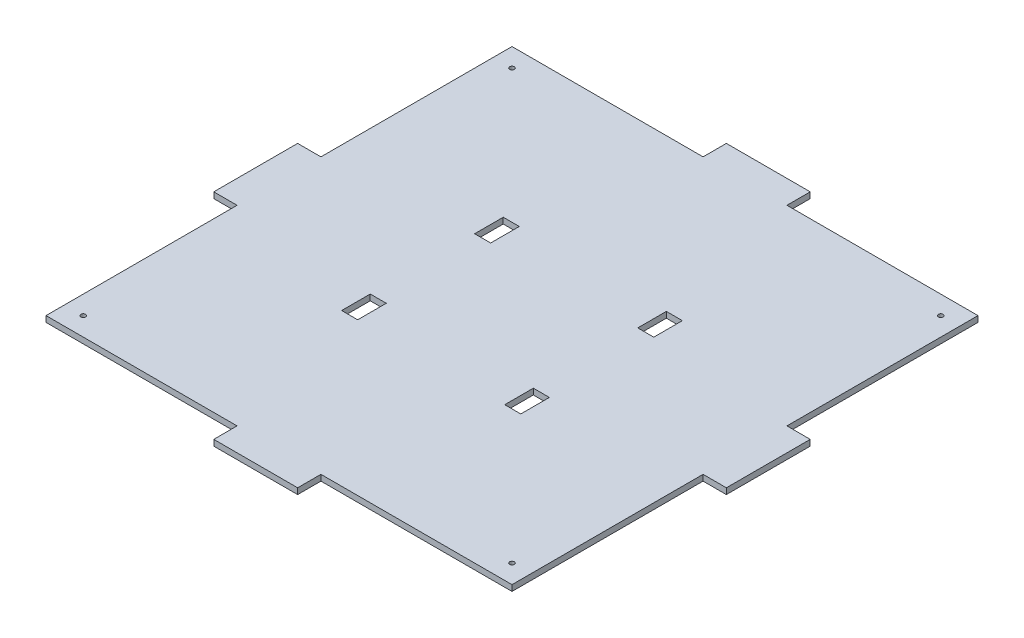
SolidWorks part; units mm, degrees
ref_plane "Front Plane" through (0, 0, 0) normal (0, 0, 1) x (1, 0, 0)
ref_plane "Top Plane" through (0, 0, 0) normal (0, 1, 0) x (1, 0, 0)
ref_plane "Right Plane" through (0, 0, 0) normal (1, 0, 0) x (0, 0, -1)
sketch "Sketch2" plane through (0, 0, 0) normal (0, 1, 0) x (1, 0, 0)
  line L1 (-125, -125) -> (125, -125)
  line L2 (-125, -125) -> (-125, 125)
  line L3 (-125, 125) -> (125, 125)
  line L4 (125, -125) -> (125, 125)
  line L5 (-125, -125) -> (125, 125) construction
  line L6 (-125, 125) -> (125, -125) construction
  point P0 (0, 0)
  dimension "D1" = 250
  dimension "250" = 250
extrude "Boss-Extrude1" add sketch "Sketch2" along normal blind 3.175
sketch "Sketch3" plane through (0, 3.175, 0) normal (0, 1, 0) x (1, 0, 0)
  line L0 (-125, 0) -> (125, 0) construction
  line L1 (-125, 125) -> (-125, -125) construction
  line L2 (125, -125) -> (125, 125) construction
  line L3 (-43.75, 125) -> (-43.75, -125) construction
  line L4 (125, 125) -> (-125, 125) construction
  line L5 (-125, -125) -> (125, -125) construction
  line L6 (0, 125) -> (0, -125) construction
  line L11 (-48.05, 28) -> (-39.45, 28)
  line L12 (-48.05, 28) -> (-48.05, 43.35)
  line L13 (-48.05, 43.35) -> (-39.45, 43.35)
  line L14 (-39.45, 28) -> (-39.45, 43.35)
  line L15 (-48.05, 28) -> (-39.45, 43.35) construction
  line L16 (-48.05, 43.35) -> (-39.45, 28) construction
  line L21 (-48.05, -43.35) -> (-39.45, -43.35)
  line L22 (-48.05, -43.35) -> (-48.05, -28)
  line L23 (-48.05, -28) -> (-39.45, -28)
  line L24 (-39.45, -43.35) -> (-39.45, -28)
  line L25 (-48.05, -43.35) -> (-39.45, -28) construction
  line L26 (-48.05, -28) -> (-39.45, -43.35) construction
  line L27 (48.05, -28) -> (39.45, -28)
  line L28 (39.45, -43.35) -> (39.45, -28)
  line L29 (48.05, -43.35) -> (39.45, -43.35)
  line L30 (48.05, -43.35) -> (48.05, -28)
  line L31 (48.05, 43.35) -> (39.45, 43.35)
  line L32 (39.45, 28) -> (39.45, 43.35)
  line L33 (48.05, 28) -> (39.45, 28)
  line L34 (48.05, 28) -> (48.05, 43.35)
  point P12 (-43.75, 35.675)
  point P17 (-43.75, -35.675)
  dimension "D1" = 43.75
  dimension "D2" = 8.6
  dimension "D3" = 15.35
  dimension "D4" = 56
  dimension "D5" = 28
extrude "Cut-Extrude1" cut sketch "Sketch3" against normal blind 10
sketch "Sketch10" plane through (0, 0, -125) normal (0, 0, -1) x (-1, 0, 0)
  line L0 (-125, 1.5875) -> (125, 1.5875) construction
  line L1 (-125, 3.175) -> (-125, 0) construction
  line L2 (125, 3.175) -> (125, 0) construction
  line L8 (-125, 3.175) -> (125, 3.175) construction
  line L9 (-22.5, 0) -> (22.5, 0)
  line L10 (-22.5, 0) -> (-22.5, 3.175)
  line L11 (-22.5, 3.175) -> (22.5, 3.175)
  line L12 (22.5, 0) -> (22.5, 3.175)
  line L13 (-22.5, 0) -> (22.5, 3.175) construction
  line L14 (-22.5, 3.175) -> (22.5, 0) construction
  point P6 (0, 1.5875)
  dimension "D1" = 45
extrude "Boss-Extrude2" add sketch "Sketch10" along normal blind 12.5
sketch "Sketch11" plane through (-125, 0, 0) normal (-1, 0, 0) x (0, 0, 1)
  line L0 (-125, 1.5875) -> (125, 1.5875) construction
  line L1 (-125, 3.175) -> (-125, 0) construction
  line L2 (125, 3.175) -> (125, 0) construction
  line L9 (-22.5, 0) -> (22.5, 0)
  line L10 (-22.5, 0) -> (-22.5, 3.175)
  line L11 (-22.5, 3.175) -> (22.5, 3.175)
  line L12 (22.5, 0) -> (22.5, 3.175)
  line L13 (-22.5, 0) -> (22.5, 3.175) construction
  line L14 (-22.5, 3.175) -> (22.5, 0) construction
  point P6 (0, 1.5875)
  dimension "D1" = 45
  dimension "D2" = 3.175
extrude "Boss-Extrude3" add sketch "Sketch11" along normal blind 12.5
sketch "Sketch13" plane through (0, 0, 125) normal (0, 0, 1) x (1, 0, 0)
  line L0 (-125, 1.5875) -> (125, 1.5875) construction
  line L3 (-125, 0) -> (-125, 3.175) construction
  line L9 (-22.5, 0) -> (22.5, 0)
  line L10 (-22.5, 0) -> (-22.5, 3.175)
  line L11 (-22.5, 3.175) -> (22.5, 3.175)
  line L12 (22.5, 0) -> (22.5, 3.175)
  line L13 (-22.5, 0) -> (22.5, 3.175) construction
  line L14 (-22.5, 3.175) -> (22.5, 0) construction
  line L15 (125, 3.175) -> (125, 0) construction
  point P6 (0, 1.5875)
  dimension "D1" = 45
  dimension "D2" = 3.175
extrude "Boss-Extrude4" add sketch "Sketch13" along normal blind 12.5
sketch "Sketch14" plane through (125, 0, 0) normal (1, 0, 0) x (0, 0, -1)
  line L0 (-125, 1.5875) -> (125, 1.5875) construction
  line L3 (-125, 3.175) -> (-125, 0) construction
  line L9 (-22.5, 0) -> (22.5, 0)
  line L10 (-22.5, 0) -> (-22.5, 3.175)
  line L11 (-22.5, 3.175) -> (22.5, 3.175)
  line L12 (22.5, 0) -> (22.5, 3.175)
  line L13 (-22.5, 0) -> (22.5, 3.175) construction
  line L14 (-22.5, 3.175) -> (22.5, 0) construction
  line L15 (125, 3.175) -> (125, 0) construction
  point P6 (0, 1.5875)
  dimension "D1" = 45
  dimension "D2" = 3.175
extrude "Boss-Extrude5" add sketch "Sketch14" along normal blind 12.5
hole_wizard "M3 Tapped Hole1" positions "3DSketch4" profile "Sketch20" tap size "M3" standard "ISO" end condition through all
sketch3d "3DSketch4"
  line L0 (-22.5, 3.175, -125) -> (-125, 3.175, -125) construction
  line L1 (-125, 3.175, -125) -> (-125, 3.175, -22.5) construction
  point P0 (-115, 3.175, -115)
  dimension "D1" = 10
  dimension "D2" = 10
sketch "Sketch20" plane through (-115, 3.175, -115) normal (1, 0, 0) x (0, 0, 1)
  line L0 (0, 0) -> (0, 3.175)
  line L1 (0, 3.175) -> (1.25, 3.175)
  line L2 (1.25, 3.175) -> (1.25, 0)
  line L5 (1.25, 0) -> (0, 0)
  line L11 (0, -6.35) -> (0, 107.95) construction
  dimension "Thru Tap Drill Dia." = 2.5
  dimension "Thru Tap Drill Depth" = 3.175
cosmetic thread "Hole Thread1" parameters "D2"=3
sketch "Sketch21" plane through (0, 3.175, 0) normal (0, 1, 0) x (1, 0, 0)
  line L0 (0, -137.5) -> (0, 137.5)
  line L1 (22.5, -137.5) -> (-22.5, -137.5) construction
  line L2 (-22.5, 137.5) -> (22.5, 137.5) construction
  line L3 (-137.5, 0) -> (137.5, 0)
  line L4 (-137.5, -22.5) -> (-137.5, 22.5) construction
  line L5 (137.5, 22.5) -> (137.5, -22.5) construction
  circle A0 centre (-115, 115) radius 1.25
  circle A1 centre (115, 115) radius 1.25
  circle A2 centre (115, -115) radius 1.25
  circle A3 centre (-115, -115) radius 1.25
extrude "Cut-Extrude2" cut sketch "Sketch21" against normal blind 10 contours A1 | A2 | A3
